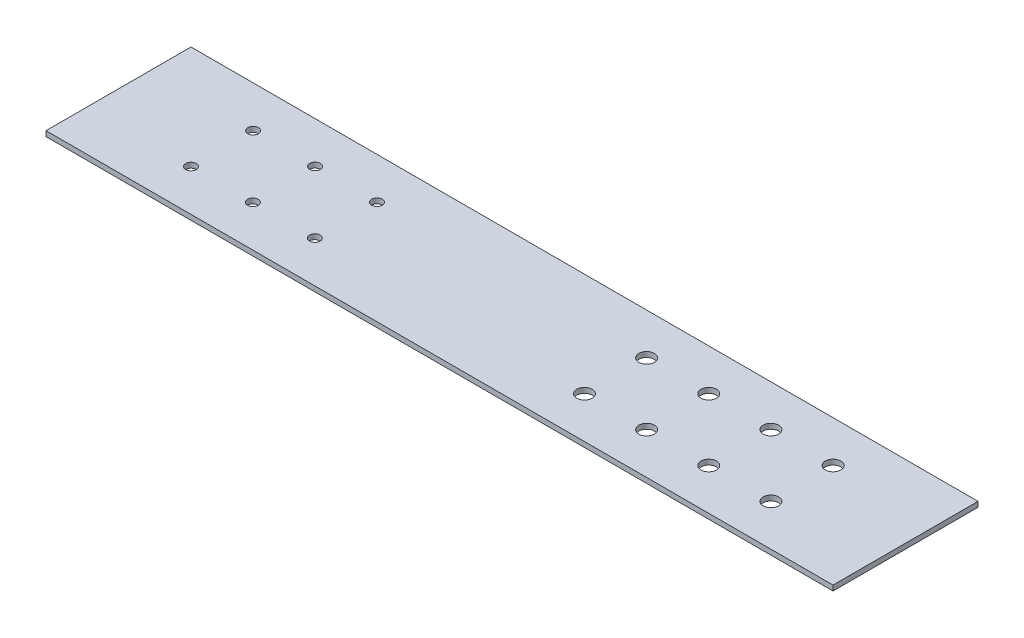
SolidWorks part; units mm, degrees
ref_plane "Front Plane" through (0, 0, 0) normal (0, 0, 1) x (1, 0, 0)
ref_plane "Top Plane" through (0, 0, 0) normal (0, 1, 0) x (1, 0, 0)
ref_plane "Right Plane" through (0, 0, 0) normal (1, 0, 0) x (0, 0, -1)
sketch "Sketch1" plane through (0, 0, 0) normal (0, 1, 0) x (1, 0, 0)
  line L1 (241.3, 44.45) -> (-241.3, 44.45)
  line L2 (241.3, 44.45) -> (241.3, -44.45)
  line L3 (241.3, -44.45) -> (-241.3, -44.45)
  line L4 (-241.3, 44.45) -> (-241.3, -44.45)
  line L5 (241.3, 44.45) -> (-241.3, -44.45) construction
  line L6 (241.3, -44.45) -> (-241.3, 44.45) construction
  point P0 (0, 0)
  dimension "D1" = 482.6
  dimension "D2" = 88.9
extrude "Boss-Extrude1" add sketch "Sketch1" along normal blind 3.175
sketch "Sketch2" plane through (0, 3.175, 0) normal (0, 1, 0) x (1, 0, 0)
  line L0 (-241.3, 44.45) -> (-241.3, -44.45) construction
  line L2 (-241.3, -44.45) -> (241.3, -44.45) construction
  circle A53 centre (-101.843, -19.05) radius 3.25
  circle A54 centre (-139.8215, -19.05) radius 3.25
  circle A55 centre (-177.8, -19.05) radius 3.25
  circle A56 centre (-139.8215, 19.05) radius 3.25
  circle A57 centre (-177.8, 19.05) radius 3.25
  circle A58 centre (-101.843, 19.05) radius 3.25
  circle A59 centre (177.8, -19.05) radius 4.7625
  circle A60 centre (139.7, -19.05) radius 4.7625
  circle A61 centre (101.6, -19.05) radius 4.7625
  circle A62 centre (63.5, -19.05) radius 4.7625
  circle A63 centre (139.7, 19.05) radius 4.7625
  circle A64 centre (101.6, 19.05) radius 4.7625
  circle A65 centre (63.5, 19.05) radius 4.7625
  circle A66 centre (177.8, 19.05) radius 4.7625
  dimension "D2" = 9.525
  dimension "D4" = 101.4785
  dimension "D5" = 139.457
  dimension "D7" = 342.9
  dimension "D6" = 304.8
  dimension "D1" = 6.5
  dimension "D3" = 63.5
  dimension "D8" = 381
  dimension "D9" = 419.1
  dimension "D10" = 25.4
  dimension "D11" = 63.5
extrude "Cut-Extrude1" cut sketch "Sketch2" against normal blind 3.175
